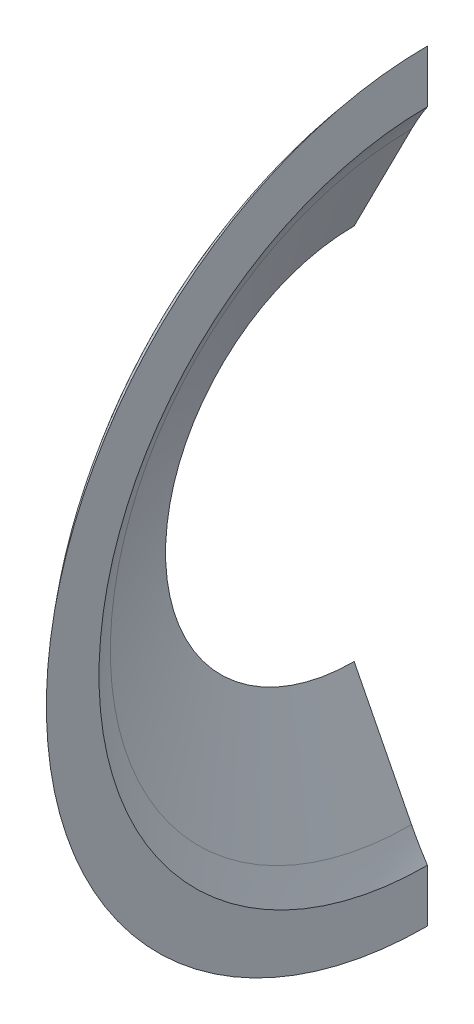
SolidWorks part; units mm, degrees
material "6061-T6 (SS)"
ref_plane "Front Plane" through (0, 0, 0) normal (0, 0, 1) x (1, 0, 0)
ref_plane "Top Plane" through (0, 0, 0) normal (0, 1, 0) x (1, 0, 0)
ref_plane "Right Plane" through (0, 0, 0) normal (1, 0, 0) x (0, 0, -1)
sketch "Sketch1" plane through (0, 0, 0) normal (0, 0, 1) x (1, 0, 0)
  line L0 (-0.2756, 0.129) -> (0.3032, 0.129)
  line L1 (-0.4012, 0.034) -> (-0.4012, 0)
  line L2 (-0.4012, 0.034) -> (-0.3773, 0.034)
  line L4 (-0.3729, 0.0367) -> (-0.3487, 0.0842)
  line L5 (-0.4012, 0) -> (0.4012, 0) construction
  line L6 (0.3794, 0.0757) -> (0.3961, 0.0297)
  line L7 (-0.4012, 0) -> (0.4012, 0)
  line L8 (0.4012, 0) -> (0.4012, 0.0006)
  arc A0 (-0.2756, 0.129) -> (-0.3487, 0.0842) centre (-0.2756, 0.047) ccw
  arc A1 (0.3032, 0.129) -> (0.3794, 0.0757) centre (0.3032, 0.048) cw
  arc A2 (0.4012, 0.0006) -> (0.3961, 0.0297) centre (0.3163, 0.0006) ccw
  arc A3 (-0.3729, 0.0367) -> (-0.3773, 0.034) centre (-0.3773, 0.039) cw
  point P6 (-0.3742, 0.034)
  dimension "D8" = 0.082
  dimension "D11" = 0.081
  dimension "D13" = 0.085
  dimension "D6" = 0.005
  dimension "D2" = 0.2756
  dimension "D3" = 0.034
  dimension "D4" = 0.3032
  dimension "D5" = 0.027
  dimension "D7" = 117
  dimension "D9" = 0.8025
  dimension "D10" = 110
revolve "Revolve2" add sketch "Sketch1" angle 360 about L7
scale "Scale1" scale about origin uniform scaling yes scale factor 649.767462
shell "Shell2" thickness 5.588
sketch "Sketch2" plane through (0, 0, 0) normal (0, 1, 0) x (1, 0, 0)
  line L7 (246.4991, 49.1898) -> (257.3884, 19.2716)
  line L8 (260.7192, 0.3818) -> (197.042, 0.3818)
  line L9 (197.042, -83.82) -> (197.042, 83.82) construction
  line L10 (197.042, 0.3818) -> (197.042, 83.82)
  line L11 (-226.5465, 54.7281) -> (-242.2713, 23.8664)
  line L12 (-260.7192, 22.0921) -> (-245.1667, 22.0921)
  line L13 (-260.7192, 22.0921) -> (-260.7192, 0)
  line L14 (-260.7192, 22.0921) -> (-260.7192, -22.0921) construction
  line L15 (-260.7192, 0) -> (-179.0728, 0)
  line L16 (-179.0728, -83.82) -> (-179.0728, 83.82) construction
  line L17 (-179.0728, 0) -> (-179.0728, 83.82)
  arc A2 (197.042, 83.82) -> (246.4991, 49.1898) centre (197.042, 31.1888) cw
  arc A3 (257.3884, 19.2716) -> (260.7192, 0.3818) centre (205.489, 0.3818) cw
  arc A4 (-179.0728, 83.82) -> (-226.5465, 54.7281) centre (-179.0728, 30.5391) ccw
  arc A5 (-242.2713, 23.8664) -> (-245.1667, 22.0921) centre (-245.1667, 25.3417) cw
revolve "Added to make cavity cut for shoulder" [suppressed] add sketch "Sketch2" angle 360 about L15
sketch "Sketch3" plane through (-260.7192, 0, 0) normal (-1, 0, 0) x (0, 0, 1)
  circle A0 centre (0, 0) radius 66.04
  circle A1 centre (0, 0) radius 101.6
  dimension "D1" = 203.2
  dimension "D2" = 132.08
extrude "Cut-Extrude2" cut sketch "Sketch3" against normal through all
sketch "Sketch4" plane through (-260.7192, 0, 0) normal (-1, 0, 0) x (0, 0, 1)
  circle A0 centre (0, 0) radius 92.0472
extrude "Cut-Extrude3" cut sketch "Sketch4" against normal blind 41.91 from offset 41.91 offset against normal yes
sketch "Sketch5" plane through (-218.8092, 0, 0) normal (1, 0, 0) x (0, 0, -1)
  circle A0 centre (0, 0) radius 73.0056
extrude "Cut-Extrude4" cut sketch "Sketch5" against normal blind 50.8 from offset 12.7 offset against normal yes
sketch "Sketch6" plane through (0, 0, 0) normal (0, 0, 1) x (1, 0, 0)
  line L1 (-545.727, 480.5422) -> (-121.6676, 480.5422)
  line L2 (-545.727, 480.5422) -> (-545.727, -209.8002)
  line L3 (-545.727, -209.8002) -> (-121.6676, -209.8002)
  line L4 (-121.6676, 480.5422) -> (-121.6676, -209.8002)
  line L5 (-545.727, 480.5422) -> (-121.6676, -209.8002) construction
  line L6 (-545.727, -209.8002) -> (-121.6676, 480.5422) construction
  point P0 (-333.6973, 135.371)
extrude "Cut-Extrude5" cut sketch "Sketch6" against normal through all
